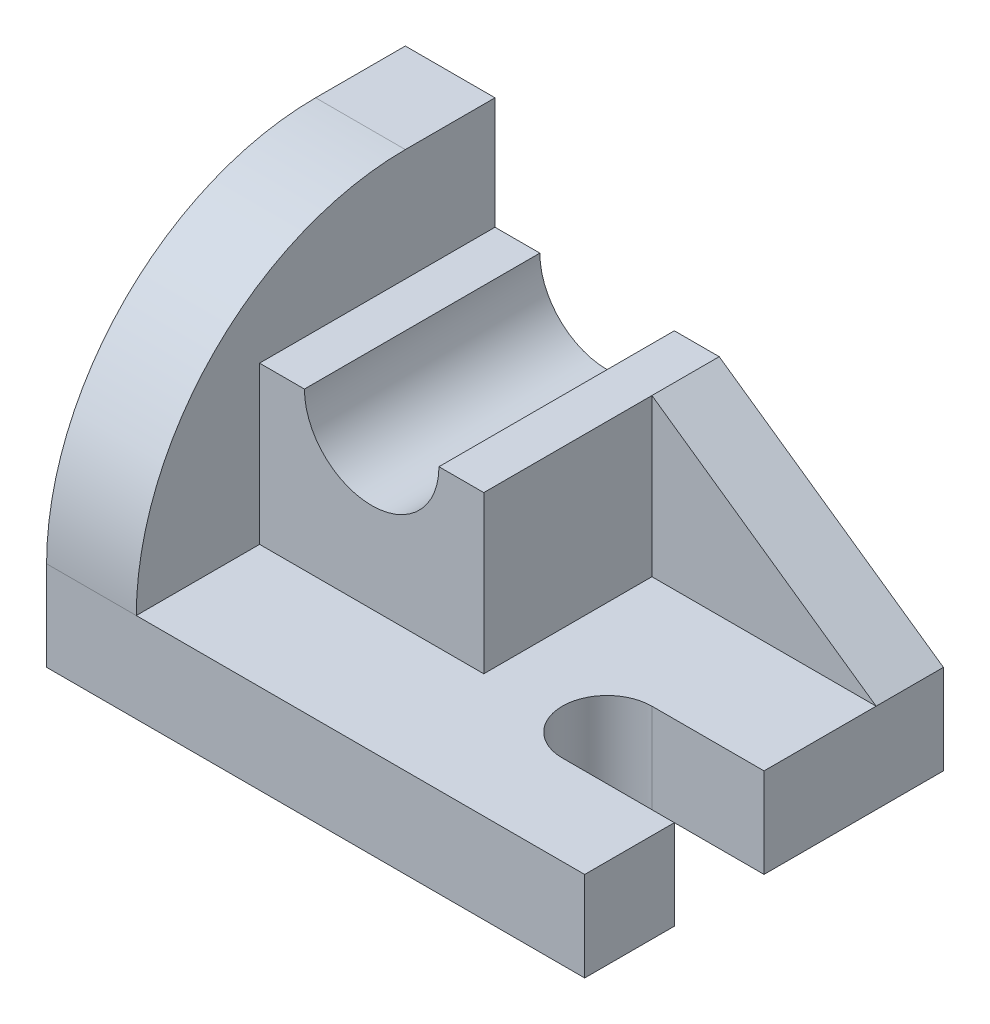
SolidWorks part; units mm, degrees
ref_plane "Front Plane" through (0, 0, 0) normal (0, 0, 1) x (1, 0, 0)
ref_plane "Top Plane" through (0, 0, 0) normal (0, 1, 0) x (1, 0, 0)
ref_plane "Right Plane" through (0, 0, 0) normal (1, 0, 0) x (0, 0, -1)
sketch "Sketch1" plane through (0, 0, 0) normal (0, 1, 0) x (1, 0, 0)
  line L1 (0, 0) -> (96, 0)
  line L2 (0, 0) -> (0, 64)
  line L3 (0, 64) -> (96, 64)
  line L4 (96, 0) -> (96, 64)
  dimension "D1" = 96
  dimension "D2" = 64
extrude "Boss-Extrude1" add sketch "Sketch1" along normal blind 16
sketch "Sketch2" plane through (0, 16, 0) normal (0, 1, 0) x (1, 0, 0)
  line L0 (96, 24) -> (76, 24) construction
  line L1 (96, 0) -> (96, 64) construction
  line L2 (96, 16) -> (76, 16)
  line L3 (96, 32) -> (76, 32)
  arc A0 (96, 16) -> (96, 32) centre (96, 24) ccw
  arc A1 (76, 32) -> (76, 16) centre (76, 24) ccw
  point P4 (86, 24)
  dimension "D2" = 8
  dimension "D1" = 20
  dimension "D3" = 16
extrude "Cut-Extrude1" cut sketch "Sketch2" against normal blind 16
sketch "Sketch3" plane through (0, 0, 0) normal (-1, 0, 0) x (0, 0, 1)
  line L1 (-64, 0) -> (0, 0)
  line L2 (-64, 0) -> (-64, 64)
  line L3 (-64, 64) -> (-48, 64)
  line L4 (0, 0) -> (0, 16)
  arc A0 (-48, 64) -> (0, 16) centre (-48, 16) cw
  point P7 (0, 64)
  dimension "D3" = 48
  dimension "D1" = 64
  dimension "D2" = 64
extrude "Boss-Extrude2" add sketch "Sketch3" against normal blind 16
sketch "Sketch4" plane through (0, 16, 0) normal (0, 1, 0) x (1, 0, 0)
  line L0 (16, 0) -> (96, 0) construction
  line L1 (16, 64) -> (56, 64)
  line L2 (16, 64) -> (16, 22)
  line L3 (16, 22) -> (56, 22)
  line L4 (56, 64) -> (56, 22)
  dimension "D1" = 40
  dimension "D2" = 22
extrude "Boss-Extrude3" add sketch "Sketch4" along normal blind 28
sketch "Sketch5" plane through (0, 0, -22) normal (0, 0, 1) x (1, 0, 0)
  line L0 (16, 44) -> (56, 44) construction
  circle A0 centre (36, 44) radius 12
  dimension "D1" = 24
extrude "Cut-Extrude2" cut sketch "Sketch5" against normal up to vertex
sketch "Sketch8" plane through (0, 0, -64) normal (0, 0, -1) x (-1, 0, 0)
  line L0 (-56, 44) -> (-96, 16)
  line L10 (-16, 44) -> (-24, 44)
  line L11 (-48, 44) -> (-56, 44)
  line L12 (-56, 44) -> (-56, 16)
  line L13 (-56, 16) -> (-96, 16)
  line L14 (-96, 16) -> (-96, 0)
  line L15 (-96, 0) -> (0, 0)
  line L16 (0, 0) -> (0, 64)
  line L17 (0, 64) -> (-16, 64)
  line L18 (-16, 64) -> (-16, 44)
  line L21 (-56, 44) -> (-56, 16)
  line L22 (-56, 16) -> (-96, 16)
  arc A1 (-48, 44) -> (-24, 44) centre (-36, 44) ccw
  dimension "D1" = 0
extrude "Boss-Extrude4" add sketch "Sketch8" against normal blind 12
